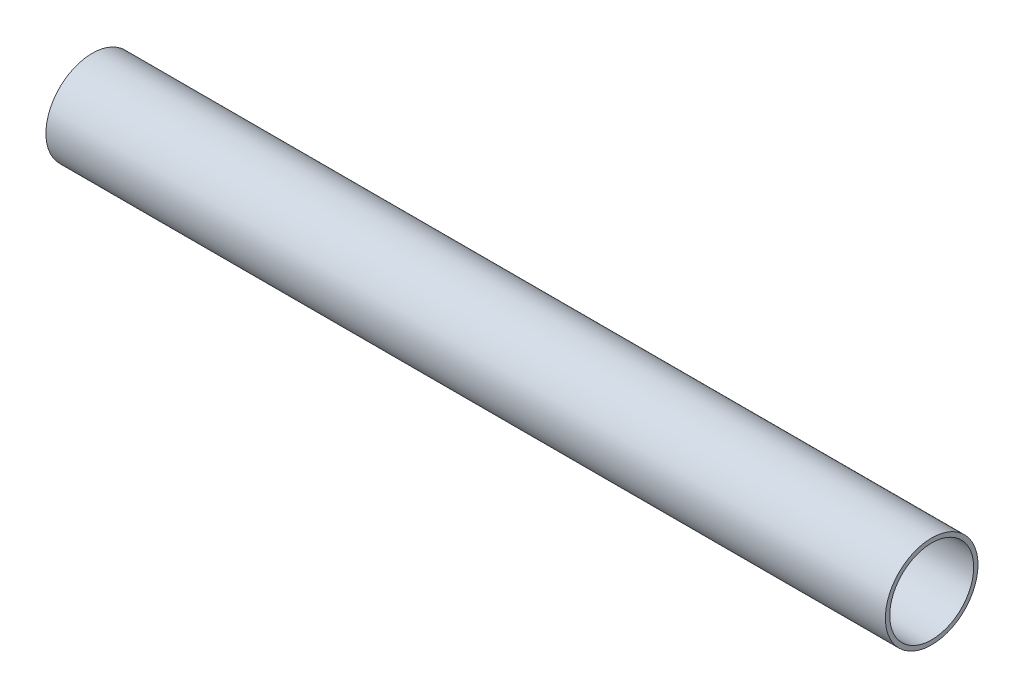
SolidWorks part; units mm, degrees
material "2024 Alloy"
ref_plane "Front Plane" through (0, 0, 0) normal (0, 0, 1) x (1, 0, 0)
ref_plane "Top Plane" through (0, 0, 0) normal (0, 1, 0) x (1, 0, 0)
ref_plane "Right Plane" through (0, 0, 0) normal (1, 0, 0) x (0, 0, -1)
sketch "Sketch1" plane through (0, 0, 0) normal (0, 0, 1) x (1, 0, 0)
  line L0 (0, 8) -> (0, 7.25)
  line L1 (0, 7.25) -> (145, 7.25)
  line L2 (145, 7.25) -> (145, 8)
  line L3 (145, 8) -> (0, 8)
  line L4 (0, 0) -> (145, 0) construction
revolve "Revolve1" add sketch "Sketch1" angle 360 about L4
